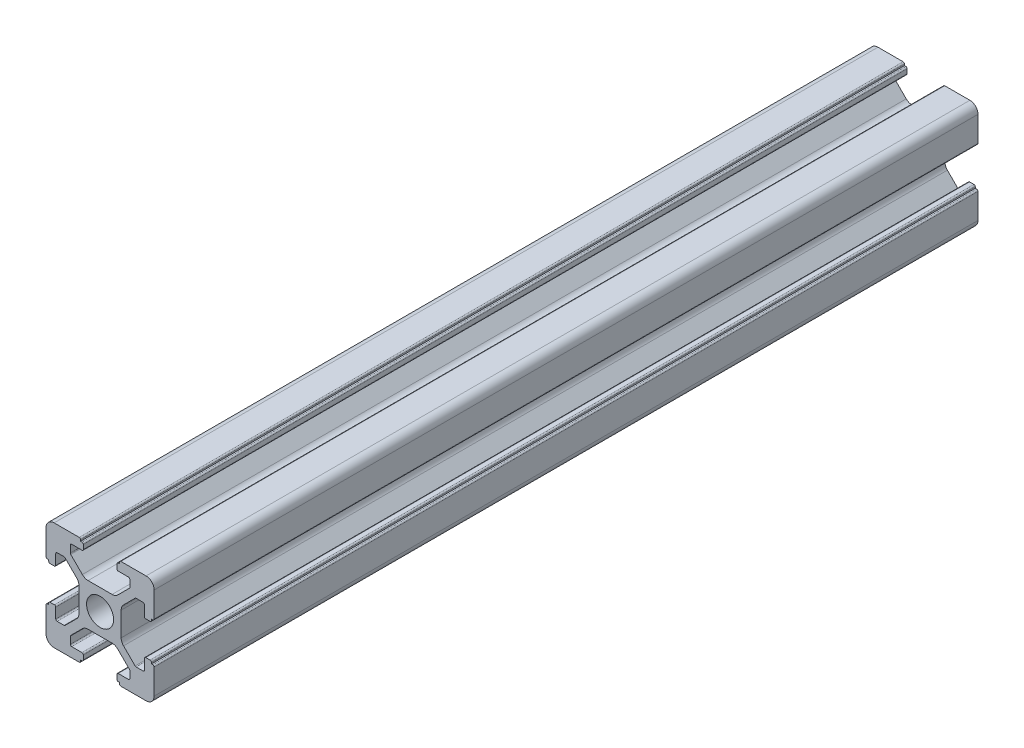
SolidWorks part; units mm, degrees
material "1060 Alloy"
ref_plane "前视基准面" through (0, 0, 0) normal (0, 0, 1) x (1, 0, 0)
ref_plane "上视基准面" through (0, 0, 0) normal (0, 1, 0) x (1, 0, 0)
ref_plane "右视基准面" through (0, 0, 0) normal (1, 0, 0) x (0, 0, -1)
sketch "草图1" plane through (0, 0, 0) normal (0, 0, 1) x (1, 0, 0)
  line L0 (0, 0) -> (0, 5.5) construction
  line L1 (-8.5023, -10.0023) -> (-3.85, -10.0023)
  line L2 (-10.0023, -8.5023) -> (-10.0023, -3.85)
  line L3 (-8.5023, 10.0023) -> (-3.85, 10.0023)
  line L4 (10.0023, -8.5023) -> (10.0023, -3.85)
  line L5 (-10.0023, -10.0023) -> (10.0023, 10.0023) construction
  line L6 (-10.0023, 10.0023) -> (10.0023, -10.0023) construction
  line L7 (-2.218, -3.9) -> (2.218, -3.9)
  line L8 (-3.9, -2.218) -> (-3.9, 2.218)
  line L9 (-2.218, 3.9) -> (2.218, 3.9)
  line L10 (3.9, -2.218) -> (3.9, 2.218)
  line L11 (-3.9, -3.9) -> (3.9, 3.9) construction
  line L12 (-3.9, 3.9) -> (3.9, -3.9) construction
  line L13 (-5.25, -8.2) -> (-3.35, -8.2)
  line L14 (-8.2, -5.25) -> (-8.2, -3.35)
  line L15 (-5.25, 8.2) -> (-3.35, 8.2)
  line L16 (8.2, -5.25) -> (8.2, -3.35)
  line L17 (-8.2, -8.2) -> (8.2, 8.2) construction
  line L18 (-8.2, 8.2) -> (8.2, -8.2) construction
  line L19 (-7.95, 5.5) -> (-6.6642, 5.5)
  line L20 (0, 0) -> (5.5, 0) construction
  line L23 (-5.5, 7.95) -> (-5.5, 6.6642)
  line L26 (0, 0) -> (-0.5303, 0.5303)
  line L27 (3.2787, 4.3393) -> (5.4268, 6.4874)
  line L28 (0, 0) -> (0.5303, -0.5303)
  line L29 (5.5, 6.6642) -> (5.5, 7.95)
  line L30 (4.3393, 3.2787) -> (6.4874, 5.4268)
  line L31 (6.6642, 5.5) -> (7.95, 5.5)
  line L32 (4.3393, -3.2787) -> (6.4874, -5.4268)
  line L33 (3.2787, -4.3393) -> (5.4268, -6.4874)
  line L34 (-3.2787, -4.3393) -> (-5.4268, -6.4874)
  line L35 (-4.3393, -3.2787) -> (-6.4874, -5.4268)
  line L36 (-4.3393, 3.2787) -> (-6.4874, 5.4268)
  line L37 (-3.2787, 4.3393) -> (-5.4268, 6.4874)
  line L38 (3.1, -8.45) -> (3.1, -9.2523)
  line L39 (8.45, 3.1) -> (9.2523, 3.1)
  line L40 (-5.5, -6.6642) -> (-5.5, -7.95)
  line L41 (-6.6642, -5.5) -> (-7.95, -5.5)
  line L42 (5.5, -6.6642) -> (5.5, -7.95)
  line L43 (6.6642, -5.5) -> (7.95, -5.5)
  line L44 (9.2523, -3.1) -> (8.45, -3.1)
  line L46 (10.0023, 3.85) -> (10.0023, 8.5023)
  line L47 (8.2, 3.35) -> (8.2, 5.25)
  line L48 (-3.1, -9.2523) -> (-3.1, -8.45)
  line L49 (-8.45, -3.1) -> (-9.2523, -3.1)
  line L50 (-9.2523, 3.1) -> (-8.45, 3.1)
  line L51 (-3.1, 8.45) -> (-3.1, 9.2523)
  line L52 (3.1, 9.2523) -> (3.1, 8.45)
  line L53 (3.85, 10.0023) -> (8.5023, 10.0023)
  line L54 (3.35, 8.2) -> (5.25, 8.2)
  line L55 (-10.0023, 3.85) -> (-10.0023, 8.5023)
  line L56 (-8.2, 3.35) -> (-8.2, 5.25)
  line L57 (3.35, -8.2) -> (5.25, -8.2)
  line L58 (3.85, -10.0023) -> (8.5023, -10.0023)
  line L59 (9.7523, -3.6) -> (9.5023, -3.6)
  line L61 (9.7523, 3.6) -> (9.5023, 3.6)
  line L62 (9.5023, -3.6) -> (9.5023, -3.35)
  line L63 (3.6, -9.7523) -> (3.6, -9.5023)
  line L64 (3.35, -9.5023) -> (3.6, -9.5023)
  line L65 (9.5023, 3.35) -> (9.5023, 3.6)
  line L66 (-3.6, -9.5023) -> (-3.35, -9.5023)
  line L67 (-3.6, -9.7523) -> (-3.6, -9.5023)
  line L68 (-9.7523, -3.6) -> (-9.5023, -3.6)
  line L69 (-9.5023, -3.35) -> (-9.5023, -3.6)
  line L70 (-9.5023, 3.6) -> (-9.5023, 3.35)
  line L71 (-9.7523, 3.6) -> (-9.5023, 3.6)
  line L72 (-3.6, 9.7523) -> (-3.6, 9.5023)
  line L73 (-3.35, 9.5023) -> (-3.6, 9.5023)
  line L74 (3.6, 9.5023) -> (3.35, 9.5023)
  line L75 (3.6, 9.7523) -> (3.6, 9.5023)
  circle A0 centre (0, 0) radius 2.5
  arc A1 (10.0023, 8.5023) -> (8.5023, 10.0023) centre (8.5023, 8.5023) ccw
  arc A2 (8.5023, -10.0023) -> (10.0023, -8.5023) centre (8.5023, -8.5023) ccw
  arc A3 (-10.0023, -8.5023) -> (-8.5023, -10.0023) centre (-8.5023, -8.5023) ccw
  arc A4 (-10.0023, 8.5023) -> (-8.5023, 10.0023) centre (-8.5023, 8.5023) cw
  arc A5 (-9.5023, -3.35) -> (-9.2523, -3.1) centre (-9.2523, -3.35) cw
  arc A6 (-9.7523, -3.6) -> (-10.0023, -3.85) centre (-9.7523, -3.85) ccw
  arc A7 (-8.45, -3.1) -> (-8.2, -3.35) centre (-8.45, -3.35) cw
  arc A8 (-7.95, -5.5) -> (-8.2, -5.25) centre (-7.95, -5.25) cw
  arc A9 (-6.4874, -5.4268) -> (-6.6642, -5.5) centre (-6.6642, -5.25) cw
  arc A10 (-5.4268, -6.4874) -> (-5.5, -6.6642) centre (-5.25, -6.6642) ccw
  arc A11 (-5.5, -7.95) -> (-5.25, -8.2) centre (-5.25, -7.95) ccw
  arc A12 (-3.6, -9.7523) -> (-3.85, -10.0023) centre (-3.85, -9.7523) cw
  arc A13 (-3.35, -9.5023) -> (-3.1, -9.2523) centre (-3.35, -9.2523) ccw
  arc A14 (-3.1, -8.45) -> (-3.35, -8.2) centre (-3.35, -8.45) ccw
  arc A15 (3.1, -8.45) -> (3.35, -8.2) centre (3.35, -8.45) cw
  arc A16 (5.5, -7.95) -> (5.25, -8.2) centre (5.25, -7.95) cw
  arc A17 (5.4268, -6.4874) -> (5.5, -6.6642) centre (5.25, -6.6642) cw
  arc A18 (6.4874, -5.4268) -> (6.6642, -5.5) centre (6.6642, -5.25) ccw
  arc A19 (7.95, -5.5) -> (8.2, -5.25) centre (7.95, -5.25) ccw
  arc A20 (8.45, -3.1) -> (8.2, -3.35) centre (8.45, -3.35) ccw
  arc A21 (9.5023, -3.35) -> (9.2523, -3.1) centre (9.2523, -3.35) ccw
  arc A22 (9.7523, -3.6) -> (10.0023, -3.85) centre (9.7523, -3.85) cw
  arc A23 (3.35, -9.5023) -> (3.1, -9.2523) centre (3.35, -9.2523) cw
  arc A24 (3.6, -9.7523) -> (3.85, -10.0023) centre (3.85, -9.7523) ccw
  arc A25 (7.95, 5.5) -> (8.2, 5.25) centre (7.95, 5.25) cw
  arc A26 (8.2, 3.35) -> (8.45, 3.1) centre (8.45, 3.35) ccw
  arc A27 (9.5023, 3.35) -> (9.2523, 3.1) centre (9.2523, 3.35) cw
  arc A28 (9.7523, 3.6) -> (10.0023, 3.85) centre (9.7523, 3.85) ccw
  arc A29 (6.6642, 5.5) -> (6.4874, 5.4268) centre (6.6642, 5.25) ccw
  arc A30 (5.4268, 6.4874) -> (5.5, 6.6642) centre (5.25, 6.6642) ccw
  arc A31 (5.5, 7.95) -> (5.25, 8.2) centre (5.25, 7.95) ccw
  arc A32 (3.1, 8.45) -> (3.35, 8.2) centre (3.35, 8.45) ccw
  arc A33 (3.6, 9.7523) -> (3.85, 10.0023) centre (3.85, 9.7523) cw
  arc A34 (3.35, 9.5023) -> (3.1, 9.2523) centre (3.35, 9.2523) ccw
  arc A35 (-9.7523, 3.6) -> (-10.0023, 3.85) centre (-9.7523, 3.85) cw
  arc A36 (-9.5023, 3.35) -> (-9.2523, 3.1) centre (-9.2523, 3.35) ccw
  arc A37 (-8.45, 3.1) -> (-8.2, 3.35) centre (-8.45, 3.35) ccw
  arc A38 (-8.2, 5.25) -> (-7.95, 5.5) centre (-7.95, 5.25) cw
  arc A39 (-6.4874, 5.4268) -> (-6.6642, 5.5) centre (-6.6642, 5.25) ccw
  arc A40 (-5.4268, 6.4874) -> (-5.5, 6.6642) centre (-5.25, 6.6642) cw
  arc A41 (-5.5, 7.95) -> (-5.25, 8.2) centre (-5.25, 7.95) cw
  arc A42 (-3.1, 8.45) -> (-3.35, 8.2) centre (-3.35, 8.45) cw
  arc A43 (-3.1, 9.2523) -> (-3.35, 9.5023) centre (-3.35, 9.2523) ccw
  arc A44 (-3.6, 9.7523) -> (-3.85, 10.0023) centre (-3.85, 9.7523) ccw
  arc A45 (-4.3393, 3.2787) -> (-3.9, 2.218) centre (-5.4, 2.218) cw
  arc A46 (-3.2787, 4.3393) -> (-2.218, 3.9) centre (-2.218, 5.4) ccw
  arc A47 (3.2787, 4.3393) -> (2.218, 3.9) centre (2.218, 5.4) cw
  arc A48 (4.3393, 3.2787) -> (3.9, 2.218) centre (5.4, 2.218) ccw
  arc A49 (4.3393, -3.2787) -> (3.9, -2.218) centre (5.4, -2.218) cw
  arc A50 (3.2787, -4.3393) -> (2.218, -3.9) centre (2.218, -5.4) ccw
  arc A51 (-4.3393, -3.2787) -> (-3.9, -2.218) centre (-5.4, -2.218) ccw
  arc A52 (-2.218, -3.9) -> (-3.2787, -4.3393) centre (-2.218, -5.4) ccw
  point P0 (0, 0)
  point P7 (10.0023, 0)
  point P62 (0, 0)
  point P76 (0, 0)
  point P92 (-8.2, -5.5)
  point P99 (0, 0)
  point P106 (-5.5, -8.2)
  point P117 (5.5, -8.2)
  point P124 (8.2, -5.5)
  point P137 (8.2, 5.5)
  point P140 (8.2, 3.1)
  point P147 (6.5607, 5.5)
  point P152 (5.5, 8.2)
  point P167 (-8.2, 5.5)
  point P174 (-5.5, 8.2)
  dimension "D1" = 1.5
  dimension "D5" = 0.25
  dimension "D6" = 1.5
  dimension "D2" = 4
  dimension "D3" = 4
  dimension "D4" = 4
extrude "凸台-拉伸1" add sketch "草图1" along normal blind 152.4 contours A52 L7 A50 L33 A17 L42 A16 L57 A15 L38 A23 L64 L63 A24 L58 A2 L4 A22 L59 L62 A21 L44 A20 L16 A19 L43 A18 L32 A49 L10 A48 L30 A29 L31 A25 L47 A26 L39 A27 L65 L61 A28 L46 A1 L53 A33 L75 L74 A34 L52 A32
ref_plane "Plane1" through (0, 0, 76.2) normal (0, 0, 1) x (1, 0, 0)
